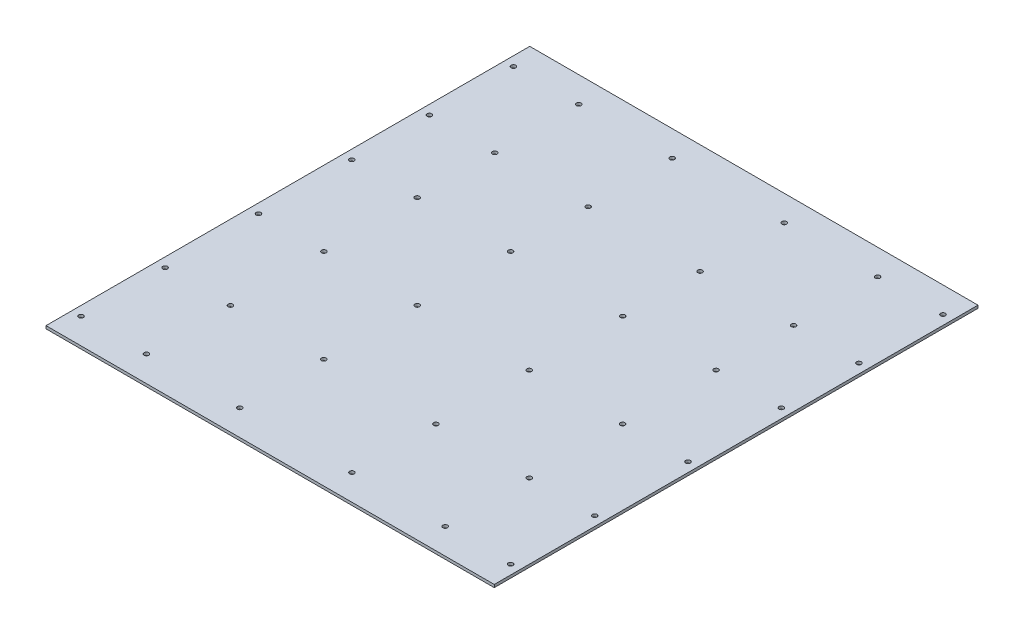
SolidWorks part; units mm, degrees
ref_plane "Alzado" through (0, 0, 0) normal (0, 0, 1) x (1, 0, 0)
ref_plane "Planta" through (0, 0, 0) normal (0, 1, 0) x (1, 0, 0)
ref_plane "Vista lateral" through (0, 0, 0) normal (1, 0, 0) x (0, 0, -1)
sketch "Croquis1" plane through (0, 0, 0) normal (0, 1, 0) x (1, 0, 0)
  line L1 (240, -259) -> (-240, -259)
  line L2 (240, -259) -> (240, 259)
  line L3 (240, 259) -> (-240, 259)
  line L4 (-240, -259) -> (-240, 259)
  line L5 (240, -259) -> (-240, 259) construction
  line L6 (240, 259) -> (-240, -259) construction
  point P0 (0, 0)
  dimension "D1" = 480
  dimension "D2" = 518
extrude "Saliente-Extruir1" add sketch "Croquis1" along normal blind 3
sketch "Croquis4" plane through (0, 3, 0) normal (0, 1, 0) x (1, 0, 0)
  line L0 (-230, 259) -> (-230, -259) construction
  line L1 (240, 259) -> (-240, 259) construction
  line L2 (-240, -259) -> (240, -259) construction
  line L3 (230, 259) -> (230, -259) construction
  line L4 (-240, 259) -> (-240, -259) construction
  line L5 (240, -259) -> (240, 259) construction
  line L6 (-230, 249) -> (230, 249) construction
  line L7 (-230, -251.5) -> (230, -251.5) construction
  line L8 (230, 0) -> (-230, 0) construction
  line L9 (0, 259) -> (0, -259) construction
  circle A0 centre (-230, -231.5) radius 2.5
  circle A1 centre (-230, 231.5) radius 2.5
  circle A2 centre (-230, -141.5) radius 2.5
  circle A3 centre (-230, 141.5) radius 2.5
  circle A4 centre (-230, -41.5) radius 2.5
  circle A5 centre (-230, 58.5) radius 2.5
  circle A6 centre (-160, 231.5) radius 2.5
  circle A7 centre (-160, 141.5) radius 2.5
  circle A8 centre (-160, 58.5) radius 2.5
  circle A9 centre (-160, -41.5) radius 2.5
  circle A10 centre (-160, -141.5) radius 2.5
  circle A11 centre (-160, -231.5) radius 2.5
  circle A12 centre (160, -231.5) radius 2.5
  circle A13 centre (160, -141.5) radius 2.5
  circle A14 centre (160, -41.5) radius 2.5
  circle A15 centre (160, 58.5) radius 2.5
  circle A16 centre (160, 141.5) radius 2.5
  circle A17 centre (160, 231.5) radius 2.5
  circle A18 centre (230, -231.5) radius 2.5
  circle A19 centre (230, -141.5) radius 2.5
  circle A20 centre (230, -41.5) radius 2.5
  circle A21 centre (230, 58.5) radius 2.5
  circle A22 centre (230, 141.5) radius 2.5
  circle A23 centre (230, 231.5) radius 2.5
  circle A24 centre (-60, 231.5) radius 2.5
  circle A25 centre (-60, 141.5) radius 2.5
  circle A26 centre (-60, 58.5) radius 2.5
  circle A27 centre (-60, -41.5) radius 2.5
  circle A28 centre (-60, -141.5) radius 2.5
  circle A29 centre (-60, -231.5) radius 2.5
  circle A30 centre (60, -231.5) radius 2.5
  circle A31 centre (60, -141.5) radius 2.5
  circle A32 centre (60, -41.5) radius 2.5
  circle A33 centre (60, 58.5) radius 2.5
  circle A34 centre (60, 141.5) radius 2.5
  circle A35 centre (60, 231.5) radius 2.5
  point P22 (0, 0)
  dimension "D5" = 5
  dimension "D6" = 20
  dimension "D1" = 10
  dimension "D2" = 10
  dimension "D3" = 10
  dimension "D4" = 7.5
  dimension "D7" = 2
  dimension "D8" = 3
  dimension "D9" = 2
  dimension "D10" = 2
extrude "Cortar-Extruir2" cut sketch "Croquis4" against normal blind 3
